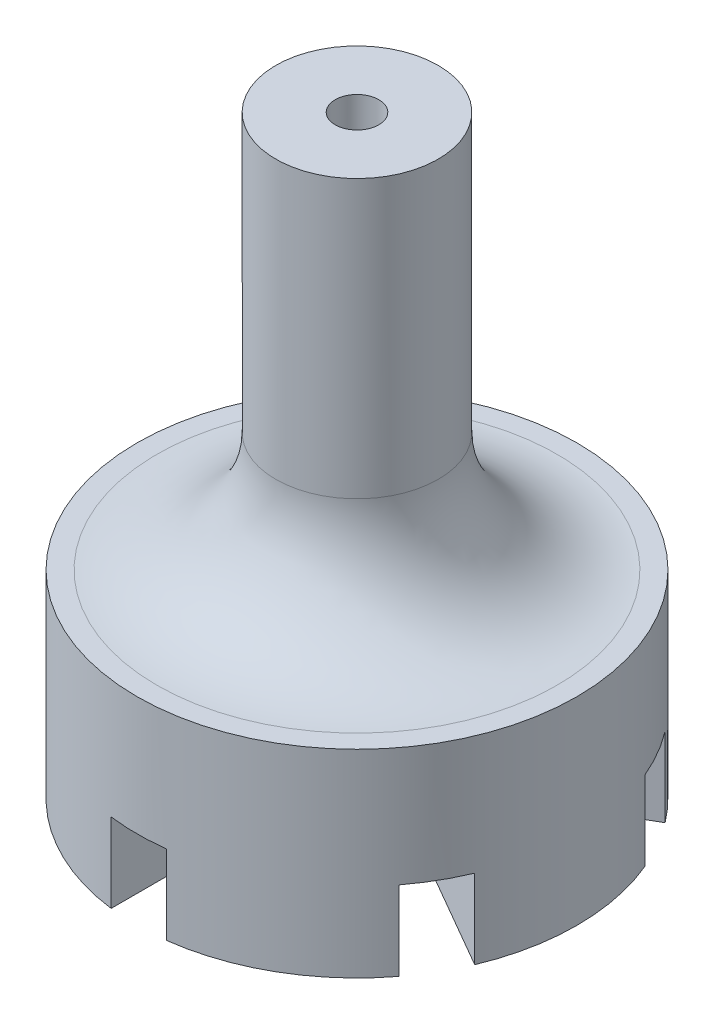
SolidWorks part; units mm, degrees
ref_plane "Plano frontal" through (0, 0, 0) normal (0, 0, 1) x (1, 0, 0)
ref_plane "Plano superior" through (0, 0, 0) normal (0, 1, 0) x (1, 0, 0)
ref_plane "Plano direito" through (0, 0, 0) normal (1, 0, 0) x (0, 0, -1)
sketch "Esboço1" plane through (0, 0, 0) normal (0, 0, 1) x (1, 0, 0)
  line L0 (0.55, 10) -> (2.05, 10)
  line L1 (2.05, 10) -> (2.05, 0)
  line L2 (2.05, 0) -> (5.55, 0)
  line L3 (5.55, 0) -> (5.55, -5)
  line L4 (5.55, -5) -> (0.55, -5)
  line L5 (0.55, -5) -> (0.55, 10)
  line L6 (0, 0) -> (0, 8860.8266) construction
  dimension "D1" = 0.55
  dimension "D2" = 1.5
  dimension "D3" = 15
  dimension "D4" = 5
  dimension "D5" = 5
revolve "Revolução1" add sketch "Esboço1" angle 360 about L6
sketch "Esboço2" plane through (0, -5, 0) normal (0, -1, 0) x (1, 0, 0)
  line L0 (-0.7, 5.55) -> (-0.7, 1.2124)
  line L3 (0.7, 5.55) -> (-0.7, 5.55)
  line L4 (5.1564, 2.1688) -> (4.4564, 3.3812)
  line L5 (4.4564, 3.3812) -> (0.7, 1.2124)
  line L8 (4.4564, -3.3812) -> (5.1564, -2.1688)
  line L9 (5.1564, -2.1688) -> (1.4, 0)
  line L12 (-0.7, -5.55) -> (0.7, -5.55)
  line L13 (0.7, -5.55) -> (0.7, -1.2124)
  line L16 (-5.1564, -2.1688) -> (-4.4564, -3.3812)
  line L17 (-4.4564, -3.3812) -> (-0.7, -1.2124)
  line L20 (-4.4564, 3.3812) -> (-5.1564, 2.1688)
  line L21 (-5.1564, 2.1688) -> (-1.4, 0)
  line L25 (-0.7, 1.2124) -> (-4.4564, 3.3812)
  line L27 (0.7, 1.2124) -> (0.7, 5.55)
  line L29 (1.4, 0) -> (5.1564, 2.1688)
  line L31 (0.7, -1.2124) -> (4.4564, -3.3812)
  line L33 (-0.7, -1.2124) -> (-0.7, -5.55)
  line L35 (-1.4, 0) -> (-5.1564, -2.1688)
  circle A0 centre (0, 0) radius 5.55 construction
  point P2 (0, 5.55)
  point P31 (0, 0)
  dimension "D1" = 1.4
  dimension "D2" = 6
extrude "Corte-extrusão2" cut sketch "Esboço2" against normal blind 2
fillet "Filete1" radius 3 1 edges at (0, 0, -2.05)
